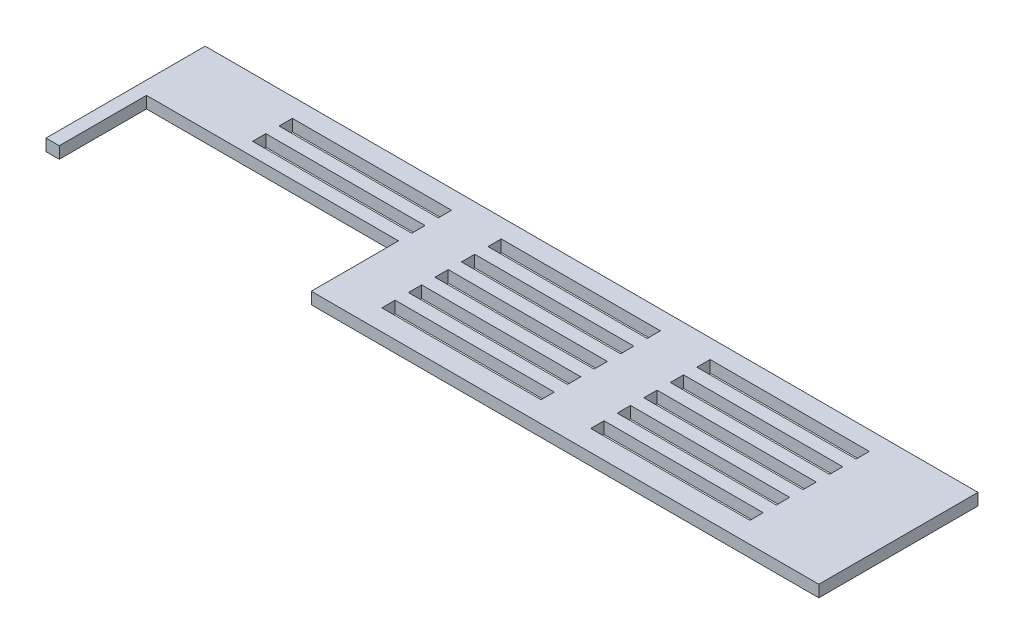
SolidWorks part; units mm, degrees
material "Acrylic (Medium-high impact)"
ref_plane "Front Plane" through (0, 0, 0) normal (0, 0, 1) x (1, 0, 0)
ref_plane "Top Plane" through (0, 0, 0) normal (0, 1, 0) x (1, 0, 0)
ref_plane "Right Plane" through (0, 0, 0) normal (1, 0, 0) x (0, 0, -1)
sketch "Sketch1" plane through (0, 0, 0) normal (0, 1, 0) x (1, 0, 0)
  line L0 (-185, -73.025) -> (185, -73.025)
  line L1 (175, 3.175) -> (-175, 3.175)
  line L2 (-185, -6.825) -> (-185, 3.175)
  line L3 (168.65, -3.175) -> (-168.65, -3.175) construction
  line L4 (-185, 3.175) -> (-175, 3.175)
  line L5 (175, 3.175) -> (185, 3.175)
  line L6 (185, 3.175) -> (185, -6.825)
  line L8 (-185, -6.825) -> (-185, -73.025)
  line L9 (-185, -73.025) -> (-178.65, -73.025) construction
  line L10 (-178.65, -13.175) -> (-178.65, -73.025) construction
  line L12 (185, -6.825) -> (185, -73.025)
  line L13 (185, -73.025) -> (178.65, -73.025) construction
  line L14 (178.65, -13.175) -> (178.65, -73.025) construction
  arc A0 (168.65, -3.175) -> (178.65, -13.175) centre (168.65, -13.175) cw construction
  arc A1 (-168.65, -3.175) -> (-178.65, -13.175) centre (-168.65, -13.175) ccw construction
  point P0 (0, 0)
  point P17 (185, 3.175)
  point P20 (-185, 3.175)
  dimension "D10" = 10
  dimension "D2" = 370
  dimension "D3" = 76.2
  dimension "D4" = 76.2
  dimension "D5" = 185
  dimension "D6" = 3.175
  dimension "D7" = 3.175
  dimension "D8" = 6.35
  dimension "D9" = 6.35
extrude "Boss-Extrude1" add sketch "Sketch1" along normal blind 5.6388
sketch "Sketch2" plane through (0, 5.6388, 0) normal (0, 1, 0) x (1, 0, 0)
  line L1 (-185, 3.175) -> (-185, -73.025) construction
  line L2 (-185, -73.025) -> (185, -73.025) construction
  line L5 (-134.2, -56.675) -> (-58, -56.675)
  line L6 (-134.2, -56.675) -> (-134.2, -63.025)
  line L7 (-134.2, -63.025) -> (-58, -63.025)
  line L8 (-58, -56.675) -> (-58, -63.025)
  dimension "D1" = 50.8
  dimension "D2" = 6.35
  dimension "D3" = 10
  dimension "D4" = 76.2
extrude "Cut-Extrude1" cut sketch "Sketch2" against normal through all
pattern_linear "LPattern1" count 5 spacing 12.7 along (0, 0, -1) count 3 spacing 100 along (1, 0, 0) of "Cut-Extrude1"
sketch "Sketch3" plane through (0, 5.6388, 0) normal (0, 1, 0) x (1, 0, 0)
  line L0 (-185, -73.025) -> (185, -73.025) construction
  line L1 (-178.65, -73.025) -> (-58, -73.025)
  line L2 (-178.65, -73.025) -> (-178.65, -31.275)
  line L3 (-178.65, -31.275) -> (-58, -31.275)
  line L4 (-58, -73.025) -> (-58, -31.275)
  dimension "D1" = 6.35
  dimension "D2" = 41.75
  dimension "D3" = 120.65
extrude "Cut-Extrude2" cut sketch "Sketch3" against normal through all
